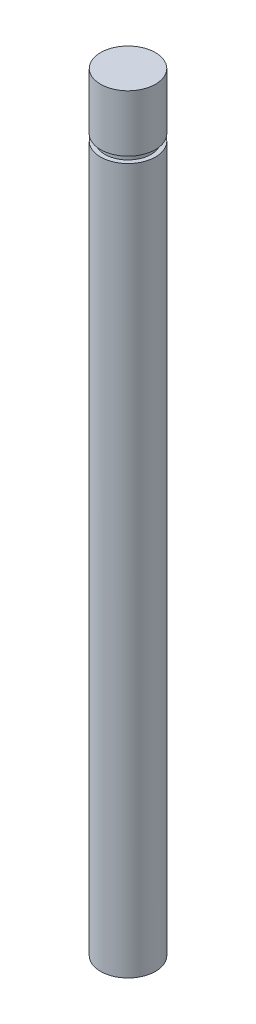
SolidWorks part; units mm, degrees
material "Plain Carbon Steel"
ref_plane "Front Plane" through (0, 0, 0) normal (0, 0, 1) x (1, 0, 0)
ref_plane "Top Plane" through (0, 0, 0) normal (0, 1, 0) x (1, 0, 0)
ref_plane "Right Plane" through (0, 0, 0) normal (1, 0, 0) x (0, 0, -1)
sketch "Sketch1" plane through (0, 0, 0) normal (0, 1, 0) x (1, 0, 0)
  circle A0 centre (0, 0) radius 3.175
  dimension "D1" = 6.35
extrude "Boss-Extrude1" add sketch "Sketch1" along normal blind 88.9
sketch "Sketch2" plane through (0, 0, 0) normal (0, -1, 0) x (1, 0, 0)
  line L0 (0, 0) -> (-2.5, 0) construction
  line L1 (-2.5, 0) -> (-2.5, -1.9572)
  line L2 (-2.5, -1.9572) -> (-3.175, -1.9572)
  line L3 (-3.175, -1.9572) -> (-3.175, 1.9572)
  line L4 (-3.175, 1.9572) -> (-2.5, 1.9572)
  line L5 (-2.5, 0) -> (-2.5, 1.9572)
  circle A0 centre (0, 0) radius 3.175 construction
  circle A1 centre (0, 0) radius 3.175 construction
  dimension "D1" = 2.5
extrude "Cut-Extrude1" cut sketch "Sketch2" against normal blind 50.8
sketch "Sketch3" plane through (0, 88.9, 0) normal (0, 1, 0) x (1, 0, 0)
  circle A0 centre (0, 0) radius 3.175 construction
  circle A1 centre (0, 0) radius 3.175
  circle A2 centre (0, 0) radius 2.667
  dimension "D1" = 5.334
extrude "Cut-Extrude2" cut sketch "Sketch3" against normal blind 0.7366 from offset 6.5532
